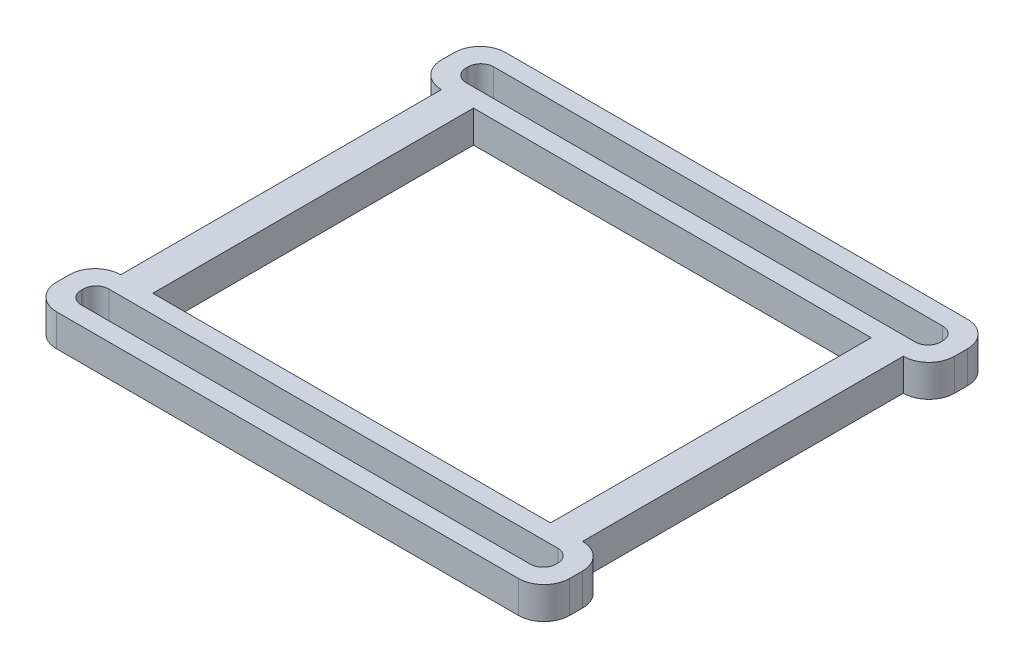
SolidWorks part; units mm, degrees
ref_plane "Plan de face" through (0, 0, 0) normal (0, 0, 1) x (1, 0, 0)
ref_plane "Plan de dessus" through (0, 0, 0) normal (0, 1, 0) x (1, 0, 0)
ref_plane "Plan de droite" through (0, 0, 0) normal (1, 0, 0) x (0, 0, -1)
sketch "Sketch1" plane through (0, 0, 0) normal (0, 1, 0) x (1, 0, 0)
  line L1 (-40, 5) -> (40, 5)
  line L2 (-40, 5) -> (-40, -5)
  line L3 (-40, -5) -> (40, -5)
  line L4 (40, 5) -> (40, -5)
  line L5 (-40, 5) -> (40, -5) construction
  line L6 (-40, -5) -> (40, 5) construction
  point P0 (0, 0)
  dimension "D1" = 10
  dimension "D2" = 80
extrude "Boss-Extrude1" add sketch "Sketch1" along normal blind 5
sketch "Sketch2" plane through (0, 5, 0) normal (0, 1, 0) x (1, 0, 0)
  line L1 (-37, 2.15) -> (37, 2.15)
  line L2 (-37, 2.15) -> (-37, -2.15)
  line L3 (-37, -2.15) -> (37, -2.15)
  line L4 (37, 2.15) -> (37, -2.15)
  line L5 (-37, 2.15) -> (37, -2.15) construction
  line L6 (-37, -2.15) -> (37, 2.15) construction
  point P0 (0, 0)
  dimension "D1" = 74
  dimension "D2" = 4.3
extrude "Cut-Extrude1" cut sketch "Sketch2" against normal blind 5
fillet "Fillet1" radius 4 4 edges at (-40, 2.5, 5) (-40, 2.5, -5) (40, 2.5, -5) (40, 2.5, 5)
fillet "Fillet2" radius 2 4 edges at (37, 2.5, 2.15) (37, 2.5, -2.15) (-37, 2.5, 2.15) (-37, 2.5, -2.15)
sketch "Sketch3" plane through (0, 0, -5) normal (0, 0, -1) x (-1, 0, 0)
  line L0 (-36, 0) -> (36, 0) construction
  line L1 (-36, 5) -> (-31, 5)
  line L2 (-36, 5) -> (-36, 0)
  line L3 (-36, 0) -> (-31, 0)
  line L4 (-31, 5) -> (-31, 0)
  line L6 (36, 5) -> (31, 5)
  line L7 (36, 5) -> (36, 0)
  line L8 (36, 0) -> (31, 0)
  line L9 (31, 5) -> (31, 0)
  dimension "D1" = 5
  dimension "D2" = 5
extrude "Boss-Extrude2" add sketch "Sketch3" along normal blind 50
ref_plane "Plane1" through (0, 0, -5) normal (0, 0, -1) x (-1, 0, 0)
ref_plane "Plane2" through (0, 0, -30) normal (0, 0, -1) x (-1, 0, 0)
mirror "Mirror1" about plane through (0, 0, -30) normal (0, 0, -1) of "Fillet2", "Fillet1", "Cut-Extrude1", "Boss-Extrude1"
